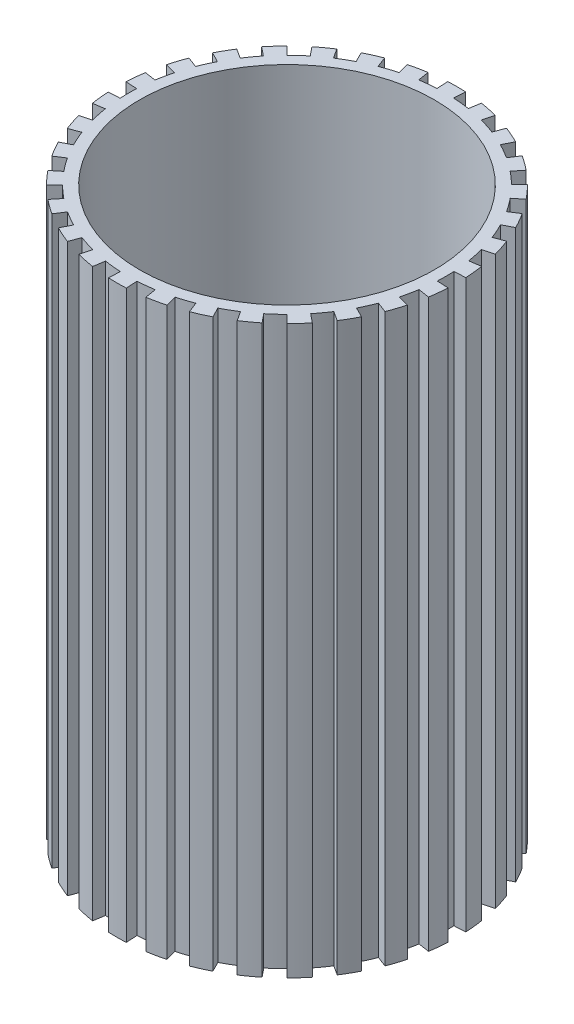
SolidWorks part; units mm, degrees
material "Rubber"
ref_plane "Front Plane" through (0, 0, 0) normal (0, 0, 1) x (1, 0, 0)
ref_plane "Top Plane" through (0, 0, 0) normal (0, 1, 0) x (1, 0, 0)
ref_plane "Right Plane" through (0, 0, 0) normal (1, 0, 0) x (0, 0, -1)
sketch "Sketch2" plane through (0, 0, 0) normal (0, 1, 0) x (1, 0, 0)
  line L0 (-11.0126, 69.1283) -> (-11.7992, 74.066)
  line L2 (-3.7264, 69.9007) -> (-3.9926, 74.8937)
  line L3 (3.6006, 69.9073) -> (3.8578, 74.9007)
  line L4 (10.8882, 69.148) -> (11.6659, 74.0871)
  line L5 (18.0565, 67.6311) -> (19.3463, 72.4619)
  line L6 (25.027, 65.3732) -> (26.8146, 70.0427)
  line L7 (31.7232, 62.399) -> (33.9892, 66.8561)
  line L8 (38.0719, 58.7412) -> (40.7913, 62.937)
  line L9 (44.0035, 54.4398) -> (47.1466, 58.3284)
  line L10 (49.4529, 49.542) -> (52.9853, 53.0807)
  line L11 (54.3606, 44.1013) -> (58.2435, 47.2514)
  line L12 (58.6726, 38.1775) -> (62.8635, 40.9045)
  line L13 (62.3418, 31.8354) -> (66.7948, 34.1094)
  line L14 (65.328, 25.1445) -> (69.9943, 26.9406)
  line L15 (67.5985, 18.1781) -> (72.4269, 19.4766)
  line L16 (69.1283, 11.0126) -> (74.066, 11.7992)
  line L17 (69.9007, 3.7264) -> (74.8937, 3.9926)
  line L18 (69.9073, -3.6006) -> (74.9007, -3.8578)
  line L19 (69.148, -10.8882) -> (74.0871, -11.6659)
  line L20 (67.6311, -18.0565) -> (72.4619, -19.3463)
  line L21 (65.3732, -25.027) -> (70.0427, -26.8146)
  line L22 (62.399, -31.7232) -> (66.8561, -33.9892)
  line L23 (58.7412, -38.0719) -> (62.937, -40.7913)
  line L24 (54.4398, -44.0035) -> (58.3284, -47.1466)
  line L25 (49.542, -49.4529) -> (53.0807, -52.9853)
  line L26 (44.1013, -54.3606) -> (47.2514, -58.2435)
  line L27 (38.1775, -58.6726) -> (40.9045, -62.8635)
  line L28 (31.8354, -62.3418) -> (34.1094, -66.7948)
  line L29 (25.1445, -65.328) -> (26.9406, -69.9943)
  line L30 (18.1781, -67.5985) -> (19.4766, -72.4269)
  line L31 (11.0126, -69.1283) -> (11.7992, -74.066)
  line L32 (3.7264, -69.9007) -> (3.9926, -74.8937)
  line L33 (-3.6006, -69.9073) -> (-3.8578, -74.9007)
  line L34 (-10.8882, -69.148) -> (-11.6659, -74.0871)
  line L35 (-18.0565, -67.6311) -> (-19.3463, -72.4619)
  line L36 (-25.027, -65.3732) -> (-26.8146, -70.0427)
  line L37 (-31.7232, -62.399) -> (-33.9892, -66.8561)
  line L38 (-38.0719, -58.7412) -> (-40.7913, -62.937)
  line L39 (-44.0035, -54.4398) -> (-47.1466, -58.3284)
  line L40 (-49.4529, -49.542) -> (-52.9853, -53.0807)
  line L41 (-54.3606, -44.1013) -> (-58.2435, -47.2514)
  line L42 (-58.6726, -38.1775) -> (-62.8635, -40.9045)
  line L43 (-62.3418, -31.8354) -> (-66.7948, -34.1094)
  line L44 (-65.328, -25.1445) -> (-69.9943, -26.9406)
  line L45 (-67.5985, -18.1781) -> (-72.4269, -19.4766)
  line L46 (-69.1283, -11.0126) -> (-74.066, -11.7992)
  line L47 (-69.9007, -3.7264) -> (-74.8937, -3.9926)
  line L48 (-69.9073, 3.6006) -> (-74.9007, 3.8578)
  line L49 (-69.148, 10.8882) -> (-74.0871, 11.6659)
  line L50 (-67.6311, 18.0565) -> (-72.4619, 19.3463)
  line L51 (-65.3732, 25.027) -> (-70.0427, 26.8146)
  line L52 (-62.399, 31.7232) -> (-66.8561, 33.9892)
  line L53 (-58.7412, 38.0719) -> (-62.937, 40.7913)
  line L54 (-54.4398, 44.0035) -> (-58.3284, 47.1466)
  line L55 (-49.542, 49.4529) -> (-53.0807, 52.9853)
  line L56 (-44.1013, 54.3606) -> (-47.2514, 58.2435)
  line L57 (-38.1775, 58.6726) -> (-40.9045, 62.8635)
  line L59 (-18.1781, 67.5985) -> (-19.4766, 72.4269)
  line L60 (0, 0) -> (-16.8797, 62.77) construction
  line L61 (0, 0) -> (-10.226, 64.1906) construction
  line L62 (-16.8797, 62.77) -> (-18.1781, 67.5985) construction
  line L63 (-10.226, 64.1906) -> (-11.0126, 69.1283) construction
  line L64 (0, 0) -> (-4.6068, 86.4158) [skipped]
  line L65 (0, 0) -> (4.4513, 86.4239) [skipped]
  line L66 (0, 0) -> (13.4607, 85.4852) [skipped]
  line L67 (0, 0) -> (22.3226, 83.6098) [skipped]
  line L68 (0, 0) -> (30.9399, 80.8185) [skipped]
  line L69 (0, 0) -> (39.2183, 77.1416) [skipped]
  line L70 (0, 0) -> (47.0669, 72.6196) [skipped]
  line L71 (0, 0) -> (54.3999, 67.302) [skipped]
  line L72 (0, 0) -> (61.1369, 61.247) [skipped]
  line L73 (0, 0) -> (67.204, 54.5209) [skipped]
  line L74 (0, 0) -> (72.5348, 47.1975) [skipped]
  line L75 (0, 0) -> (77.071, 39.357) [skipped]
  line L76 (0, 0) -> (80.7627, 31.0853) [skipped]
  line L77 (0, 0) -> (83.5696, 22.473) [skipped]
  line L78 (0, 0) -> (85.4608, 13.6145) [skipped]
  line L79 (0, 0) -> (86.4158, 4.6068) [skipped]
  line L80 (0, 0) -> (86.4239, -4.4513) [skipped]
  line L81 (0, 0) -> (85.4852, -13.4607) [skipped]
  line L82 (0, 0) -> (83.6098, -22.3226) [skipped]
  line L83 (0, 0) -> (80.8185, -30.9399) [skipped]
  line L84 (0, 0) -> (77.1416, -39.2183) [skipped]
  line L85 (0, 0) -> (72.6196, -47.0669) [skipped]
  line L86 (0, 0) -> (67.302, -54.3999) [skipped]
  line L87 (0, 0) -> (61.247, -61.1369) [skipped]
  line L88 (0, 0) -> (54.5209, -67.204) [skipped]
  line L89 (0, 0) -> (47.1975, -72.5348) [skipped]
  line L90 (0, 0) -> (39.357, -77.071) [skipped]
  line L91 (0, 0) -> (31.0853, -80.7627) [skipped]
  line L92 (0, 0) -> (22.473, -83.5696) [skipped]
  line L93 (0, 0) -> (13.6145, -85.4608) [skipped]
  line L94 (0, 0) -> (4.6068, -86.4158) [skipped]
  line L95 (0, 0) -> (-4.4513, -86.4239) [skipped]
  line L96 (0, 0) -> (-13.4607, -85.4852) [skipped]
  line L97 (0, 0) -> (-22.3226, -83.6098) [skipped]
  line L98 (0, 0) -> (-30.9399, -80.8185) [skipped]
  line L99 (0, 0) -> (-39.2183, -77.1416) [skipped]
  line L100 (0, 0) -> (-47.0669, -72.6196) [skipped]
  line L101 (0, 0) -> (-54.3999, -67.302) [skipped]
  line L102 (0, 0) -> (-61.1369, -61.247) [skipped]
  line L103 (0, 0) -> (-67.204, -54.5209) [skipped]
  line L104 (0, 0) -> (-72.5348, -47.1975) [skipped]
  line L105 (0, 0) -> (-77.071, -39.357) [skipped]
  line L106 (0, 0) -> (-80.7627, -31.0853) [skipped]
  line L107 (0, 0) -> (-83.5696, -22.473) [skipped]
  line L108 (0, 0) -> (-85.4608, -13.6145) [skipped]
  line L109 (0, 0) -> (-86.4158, -4.6068) [skipped]
  line L110 (0, 0) -> (-86.4239, 4.4513) [skipped]
  line L111 (0, 0) -> (-85.4852, 13.4607) [skipped]
  line L112 (0, 0) -> (-83.6098, 22.3226) [skipped]
  line L113 (0, 0) -> (-80.8185, 30.9399) [skipped]
  line L114 (0, 0) -> (-77.1416, 39.2183) [skipped]
  line L115 (0, 0) -> (-72.6196, 47.0669) [skipped]
  line L116 (0, 0) -> (-67.302, 54.3999) [skipped]
  line L117 (0, 0) -> (-61.247, 61.1369) [skipped]
  line L118 (0, 0) -> (-54.5209, 67.204) [skipped]
  line L119 (0, 0) -> (-47.1975, 72.5348) [skipped]
  line L120 (0, 0) -> (-31.0853, 80.7627) [skipped]
  line L121 (0, 0) -> (-39.357, 77.071) [skipped]
  line L122 (-31.8354, 62.3418) -> (-34.1094, 66.7948)
  line L123 (-25.1445, 65.328) -> (-26.9406, 69.9943)
  arc A0 (-11.7992, 74.066) -> (-19.4766, 72.4269) centre (0, 0) ccw
  arc A1 (-44.1013, 54.3606) -> (-49.542, 49.4529) centre (0, 0) ccw
  circle A2 centre (0, 0) radius 65
  arc A3 (3.8578, 74.9007) -> (-3.9926, 74.8937) centre (0, 0) ccw
  arc A5 (19.3463, 72.4619) -> (11.6659, 74.0871) centre (0, 0) ccw
  arc A6 (33.9892, 66.8561) -> (26.8146, 70.0427) centre (0, 0) ccw
  arc A7 (47.1466, 58.3284) -> (40.7913, 62.937) centre (0, 0) ccw
  arc A8 (58.2435, 47.2514) -> (52.9853, 53.0807) centre (0, 0) ccw
  arc A9 (66.7948, 34.1094) -> (62.8635, 40.9045) centre (0, 0) ccw
  arc A10 (72.4269, 19.4766) -> (69.9943, 26.9406) centre (0, 0) ccw
  arc A11 (74.8937, 3.9926) -> (74.066, 11.7992) centre (0, 0) ccw
  arc A12 (74.0871, -11.6659) -> (74.9007, -3.8578) centre (0, 0) ccw
  arc A13 (70.0427, -26.8146) -> (72.4619, -19.3463) centre (0, 0) ccw
  arc A14 (62.937, -40.7913) -> (66.8561, -33.9892) centre (0, 0) ccw
  arc A15 (53.0807, -52.9853) -> (58.3284, -47.1466) centre (0, 0) ccw
  arc A16 (40.9045, -62.8635) -> (47.2514, -58.2435) centre (0, 0) ccw
  arc A17 (26.9406, -69.9943) -> (34.1094, -66.7948) centre (0, 0) ccw
  arc A18 (11.7992, -74.066) -> (19.4766, -72.4269) centre (0, 0) ccw
  arc A19 (-3.8578, -74.9007) -> (3.9926, -74.8937) centre (0, 0) ccw
  arc A20 (-19.3463, -72.4619) -> (-11.6659, -74.0871) centre (0, 0) ccw
  arc A21 (-33.9892, -66.8561) -> (-26.8146, -70.0427) centre (0, 0) ccw
  arc A22 (-47.1466, -58.3284) -> (-40.7913, -62.937) centre (0, 0) ccw
  arc A23 (-58.2435, -47.2514) -> (-52.9853, -53.0807) centre (0, 0) ccw
  arc A24 (-66.7948, -34.1094) -> (-62.8635, -40.9045) centre (0, 0) ccw
  arc A25 (-72.4269, -19.4766) -> (-69.9943, -26.9406) centre (0, 0) ccw
  arc A26 (-74.8937, -3.9926) -> (-74.066, -11.7992) centre (0, 0) ccw
  arc A27 (-74.0871, 11.6659) -> (-74.9007, 3.8578) centre (0, 0) ccw
  arc A28 (-70.0427, 26.8146) -> (-72.4619, 19.3463) centre (0, 0) ccw
  arc A29 (-62.937, 40.7913) -> (-66.8561, 33.9892) centre (0, 0) ccw
  arc A30 (-53.0807, 52.9853) -> (-58.3284, 47.1466) centre (0, 0) ccw
  arc A31 (-40.9045, 62.8635) -> (-47.2514, 58.2435) centre (0, 0) ccw
  arc A32 (-26.9406, 69.9943) -> (-34.1094, 66.7948) centre (0, 0) ccw
  arc A33 (-38.1775, 58.6726) -> (-44.1013, 54.3606) centre (0, 0) ccw construction
  arc A34 (-31.8354, 62.3418) -> (-38.1775, 58.6726) centre (0, 0) ccw
  arc A35 (-25.1445, 65.328) -> (-31.8354, 62.3418) centre (0, 0) ccw construction
  arc A36 (-54.4398, 44.0035) -> (-58.7412, 38.0719) centre (0, 0) ccw
  arc A37 (-49.542, 49.4529) -> (-54.4398, 44.0035) centre (0, 0) ccw construction
  arc A38 (-62.399, 31.7232) -> (-65.3732, 25.027) centre (0, 0) ccw
  arc A39 (-58.7412, 38.0719) -> (-62.399, 31.7232) centre (0, 0) ccw construction
  arc A40 (-67.6311, 18.0565) -> (-69.148, 10.8882) centre (0, 0) ccw
  arc A41 (-65.3732, 25.027) -> (-67.6311, 18.0565) centre (0, 0) ccw construction
  arc A42 (-69.9073, 3.6006) -> (-69.9007, -3.7264) centre (0, 0) ccw
  arc A43 (-69.148, 10.8882) -> (-69.9073, 3.6006) centre (0, 0) ccw construction
  arc A44 (-69.1283, -11.0126) -> (-67.5985, -18.1781) centre (0, 0) ccw
  arc A45 (-69.9007, -3.7264) -> (-69.1283, -11.0126) centre (0, 0) ccw construction
  arc A46 (-65.328, -25.1445) -> (-62.3418, -31.8354) centre (0, 0) ccw
  arc A47 (-67.5985, -18.1781) -> (-65.328, -25.1445) centre (0, 0) ccw construction
  arc A48 (-58.6726, -38.1775) -> (-54.3606, -44.1013) centre (0, 0) ccw
  arc A49 (-62.3418, -31.8354) -> (-58.6726, -38.1775) centre (0, 0) ccw construction
  arc A50 (-49.4529, -49.542) -> (-44.0035, -54.4398) centre (0, 0) ccw
  arc A51 (-54.3606, -44.1013) -> (-49.4529, -49.542) centre (0, 0) ccw construction
  arc A52 (-38.0719, -58.7412) -> (-31.7232, -62.399) centre (0, 0) ccw
  arc A53 (-44.0035, -54.4398) -> (-38.0719, -58.7412) centre (0, 0) ccw construction
  arc A54 (-25.027, -65.3732) -> (-18.0565, -67.6311) centre (0, 0) ccw
  arc A55 (-10.8882, -69.148) -> (-3.6006, -69.9073) centre (0, 0) ccw
  arc A56 (3.7264, -69.9007) -> (11.0126, -69.1283) centre (0, 0) ccw
  arc A57 (18.1781, -67.5985) -> (25.1445, -65.328) centre (0, 0) ccw
  arc A58 (31.8354, -62.3418) -> (38.1775, -58.6726) centre (0, 0) ccw
  arc A59 (44.1013, -54.3606) -> (49.542, -49.4529) centre (0, 0) ccw
  arc A60 (54.4398, -44.0035) -> (58.7412, -38.0719) centre (0, 0) ccw
  arc A61 (62.399, -31.7232) -> (65.3732, -25.027) centre (0, 0) ccw
  arc A62 (67.6311, -18.0565) -> (69.148, -10.8882) centre (0, 0) ccw
  arc A63 (69.9073, -3.6006) -> (69.9007, 3.7264) centre (0, 0) ccw
  arc A64 (69.1283, 11.0126) -> (67.5985, 18.1781) centre (0, 0) ccw
  arc A65 (65.328, 25.1445) -> (62.3418, 31.8354) centre (0, 0) ccw
  arc A66 (58.6726, 38.1775) -> (54.3606, 44.1013) centre (0, 0) ccw
  arc A67 (49.4529, 49.542) -> (44.0035, 54.4398) centre (0, 0) ccw
  arc A68 (38.0719, 58.7412) -> (31.7232, 62.399) centre (0, 0) ccw
  arc A69 (-18.1781, 67.5985) -> (-25.1445, 65.328) centre (0, 0) ccw
  arc A70 (-3.7264, 69.9007) -> (-11.0126, 69.1283) centre (0, 0) ccw
  arc A71 (10.8882, 69.148) -> (3.6006, 69.9073) centre (0, 0) ccw
  arc A72 (25.027, 65.3732) -> (18.0565, 67.6311) centre (0, 0) ccw
  point P3 (-74.5821, -7.9067)
  dimension "D1" = 60
  dimension "D3" = 130
  dimension "D4" = 70
  dimension "D5" = 75
  dimension "D2" = 30
extrude "Boss-Extrude1" add sketch "Sketch2" along normal blind 250
